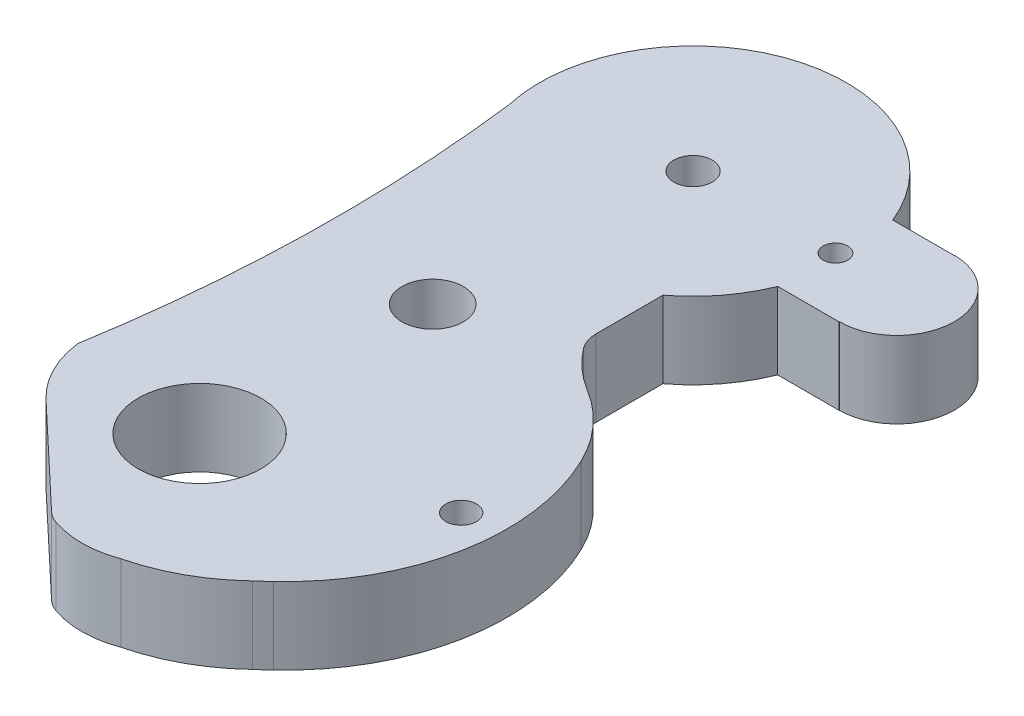
SolidWorks part; units mm, degrees
ref_plane "Front Plane" through (0, 0, 0) normal (0, 0, 1) x (1, 0, 0)
ref_plane "Top Plane" through (0, 0, 0) normal (0, 1, 0) x (1, 0, 0)
ref_plane "Right Plane" through (0, 0, 0) normal (1, 0, 0) x (0, 0, -1)
sketch "Sketch1" plane through (0, 0, 0) normal (0, 1, 0) x (1, 0, 0)
  line L0 (-16.5292, -5.1538) -> (20.4217, -5.1538) construction
  line L1 (10.2454, 19.7485) -> (14.2454, 19.7485)
  line L5 (-7.2173, -17.9903) -> (-0.4159, -24.4129)
  line L6 (7.0004, 8.0194) -> (7.0004, 3.0194)
  line L10 (10.2454, 12.2515) -> (14.2454, 12.2515)
  line L11 (14.2454, 12.2515) -> (14.2454, 12.2652)
  line L14 (14.2454, 19.7652) -> (14.2454, 19.7485)
  circle A0 centre (0, 0) radius 2
  circle A4 centre (-0.2966, -14.8977) radius 4
  arc A8 (-9.3433, -13.7957) -> (-7.2173, -17.9903) centre (-2.4427, -12.9341) ccw
  arc A9 (11.3198, -0.5063) -> (10.4714, -20.8348) centre (0.7314, -10.2463) cw
  arc A10 (10.4714, -20.8348) -> (9.7589, -21.488) centre (1.4352, -11.6928) cw
  arc A11 (-0.4159, -24.4129) -> (4.2171, -24.5326) centre (2.0482, -18.7603) ccw
  arc A12 (9.7589, -21.488) -> (4.2171, -24.5326) centre (1.2828, -12.6259) cw
  arc A13 (7.0004, 3.0194) -> (11.3198, -0.5063) centre (14.4947, 7.7922) ccw
  arc A15 (7.0004, 8.0194) -> (10.2454, 12.2515) centre (0.9746, 16) ccw
  arc A17 (-8.7715, 13.7608) -> (-9.3433, -13.7957) centre (-104.4326, 1.9618) cw
  circle A18 centre (0.9746, 16) radius 1.25
  arc A20 (10.2454, 19.7485) -> (-8.7715, 13.7608) centre (0.9746, 16) ccw
  arc A21 (14.2454, 12.2652) -> (14.2454, 19.7652) centre (14.2454, 16.0152) ccw
  circle A23 centre (10.2454, 16.0152) radius 0.8016
  circle A24 centre (12.707, -10.8463) radius 1
  point P13 (0.9746, 25.5871)
  point P35 (7.0004, 10.4214)
  point P38 (-0.4159, -24.4129)
  dimension "D1" = 50
  dimension "D2" = 20
  dimension "D3" = 2.5
  dimension "D4" = 4
  dimension "D5" = 8
  dimension "D6" = 5
  dimension "D7" = 4
  dimension "D8" = 3.75
  dimension "D9" = 1.6033
  dimension "D13" = 2
  dimension "D10" = 16
  dimension "D11" = 7
extrude "Boss-Extrude1" add sketch "Sketch1" along normal blind 5
fillet "Fillet1" radius 10 1 edges at (11.3198, 2.5, 0.5063)
fillet "Fillet2" radius 2 1 edges at (7.0004, 2.5, -3.0194)
fillet "Fillet3" radius 2 1 edges at (-0.4159, 2.5, 24.4129)
